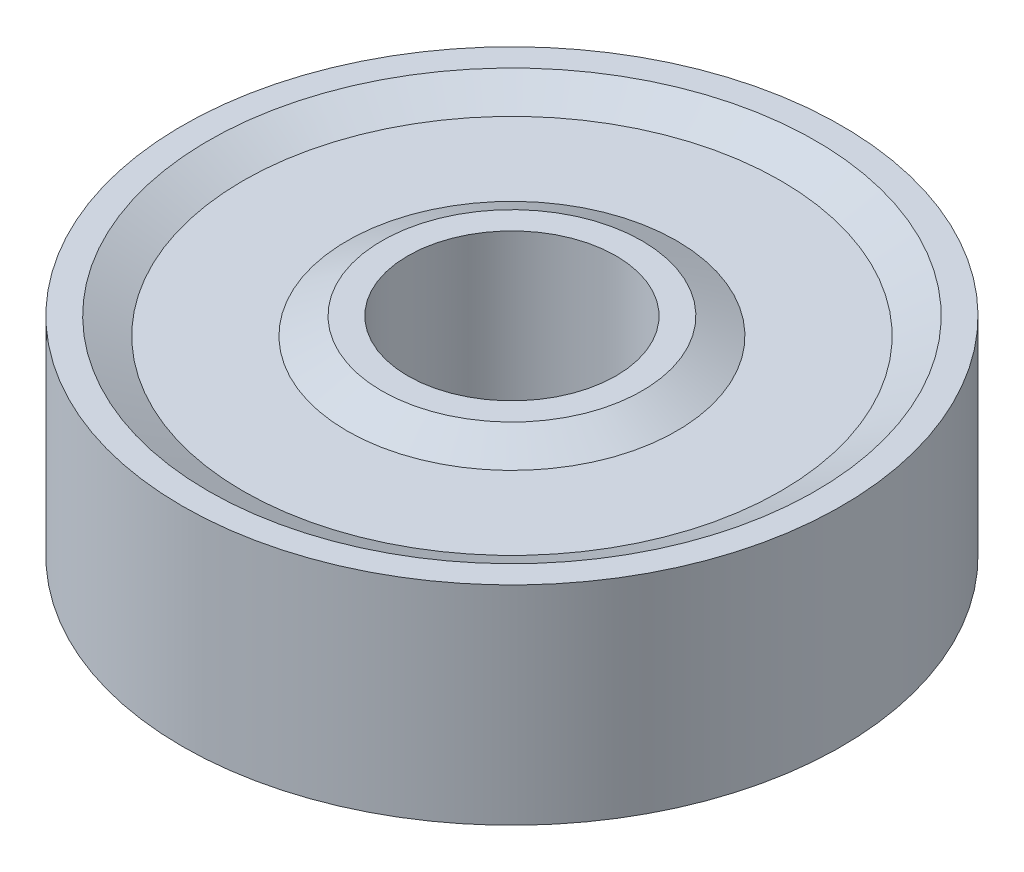
SolidWorks part; units mm, degrees
ref_plane "Front Plane" through (0, 0, 0) normal (0, 0, 1) x (1, 0, 0)
ref_plane "Top Plane" through (0, 0, 0) normal (0, 1, 0) x (1, 0, 0)
ref_plane "Right Plane" through (0, 0, 0) normal (1, 0, 0) x (0, 0, -1)
sketch "Sketch1" plane through (0, 0, 0) normal (0, 1, 0) x (1, 0, 0)
  circle A0 centre (0, 0) radius 3
  circle A1 centre (0, 0) radius 9.5
  dimension "D1" = 6
  dimension "D2" = 19
extrude "Boss-Extrude1" add sketch "Sketch1" along normal blind 6
sketch "Sketch2" plane through (0, 0, 0) normal (0, 0, 1) x (1, 0, 0)
  line L0 (-3.75, 6) -> (-4.75, 5.5)
  line L1 (9.5, 6) -> (-9.5, 6) construction
  line L2 (-4.75, 5.5) -> (-7.75, 5.5)
  line L3 (-7.75, 5.5) -> (-8.75, 6)
  line L4 (0, 6) -> (0, 0) construction
  line L5 (-9.5, 3) -> (9.5, 3) construction
  line L6 (-9.5, 6) -> (-9.5, 0) construction
  line L7 (9.5, 0) -> (9.5, 6) construction
  line L8 (-3, 6) -> (-3, 0) construction
  line L9 (-8.75, 6) -> (-3.75, 6)
  line L10 (-8.75, 0) -> (-3.75, 0)
  line L15 (-7.75, 0.5) -> (-8.75, 0)
  line L16 (-4.75, 0.5) -> (-7.75, 0.5)
  line L17 (-3.75, 0) -> (-4.75, 0.5)
  point P7 (-6.25, 5.5)
  dimension "D1" = 3
  dimension "D2" = 1
  dimension "D3" = 1
  dimension "D4" = 0.5
  dimension "D5" = 0.75
revolve "Cut-Revolve1" cut sketch "Sketch2" angle 360 about L4
